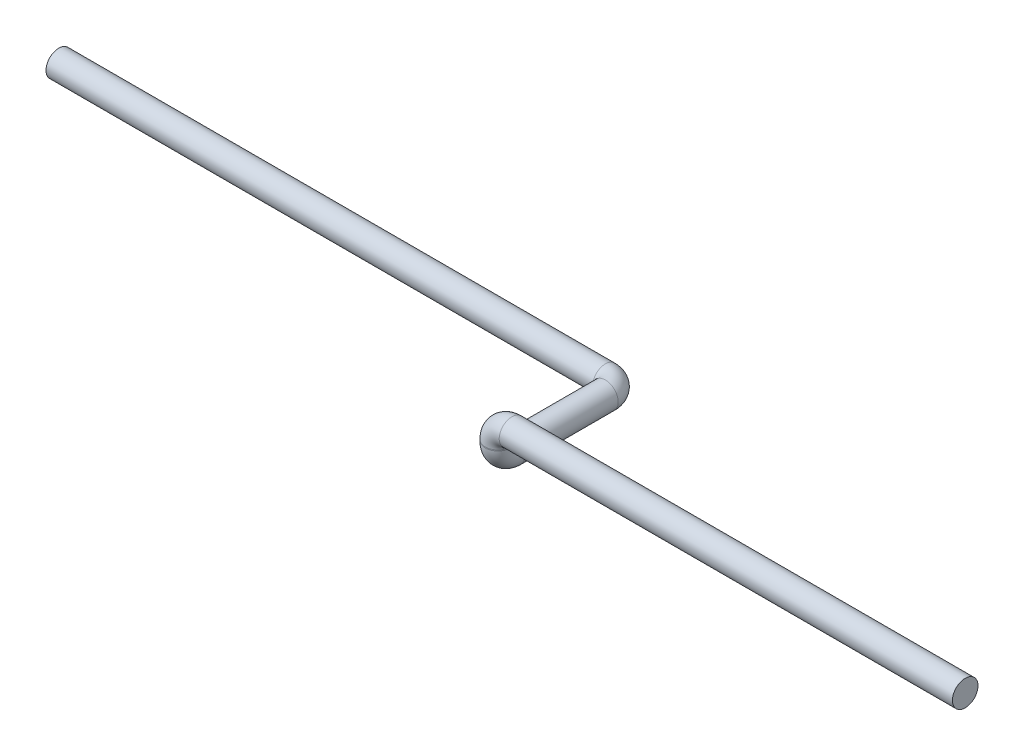
SolidWorks part; units mm, degrees
ref_plane "Alzado" through (0, 0, 0) normal (0, 0, 1) x (1, 0, 0)
ref_plane "Planta" through (0, 0, 0) normal (0, 1, 0) x (1, 0, 0)
ref_plane "Vista lateral" through (0, 0, 0) normal (1, 0, 0) x (0, 0, -1)
sketch3d "Croquis3D1"
  line L0 (0, 0, 0) -> (-485, 0, 0)
  line L1 (-500, -15, 0) -> (-500, -16, 0)
  line L2 (-500, -31, -15) -> (-500, -31, -115)
  line L3 (-515, -31, -130) -> (-1100, -31, -130)
  arc A0 (-485, 0, 0) -> (-500, -15, 0) centre (-485, -15, 0) ccw
  arc A1 (-500, -16, 0) -> (-500, -31, -15) centre (-500, -16, -15) ccw
  arc A2 (-500, -31, -115) -> (-515, -31, -130) centre (-515, -31, -115) ccw
  point P8 (-500, 0, 0)
  point P9 (-485, -15, 15)
  point P12 (-500, -31, 0)
  point P13 (-485, -16, -15)
  point P16 (-500, -31, -130)
  point P17 (-515, -16, -115)
  dimension "D1" = 500
  dimension "D2" = 31
  dimension "D5" = 15
  dimension "D3" = 130
  dimension "D4" = 600
sketch "Croquis1" plane through (0, 0, 0) normal (1, 0, 0) x (0, 0, -1)
  circle A0 centre (0, 0) radius 13.7
  dimension "D1" = 27.4
sweep "Barrer1" add profiles "Croquis1" path "Croquis3D1"
